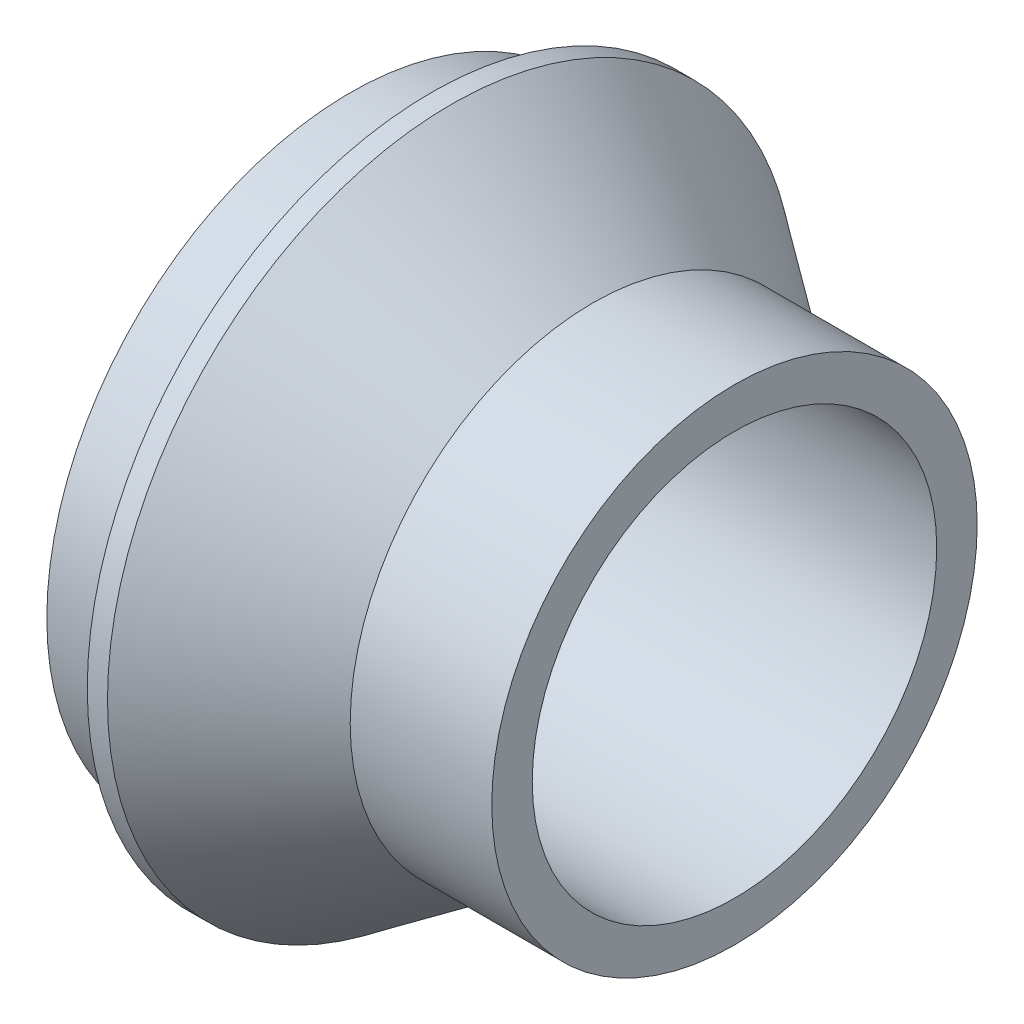
SolidWorks part; units mm, degrees
ref_plane "Płaszczyzna przednia" through (0, 0, 0) normal (0, 0, 1) x (1, 0, 0)
ref_plane "Płaszczyzna górna" through (0, 0, 0) normal (0, 1, 0) x (1, 0, 0)
ref_plane "Płaszczyzna prawa" through (0, 0, 0) normal (1, 0, 0) x (0, 0, -1)
sketch "Szkic1" plane through (0, 0, 0) normal (0, 0, 1) x (1, 0, 0)
  line L0 (0, 0) -> (42.2065, 0) construction
  line L1 (0, 15) -> (4, 15)
  line L2 (0, 13) -> (4, 13)
  line L3 (4, 13) -> (4, 10)
  line L4 (4, 10) -> (19, 10)
  line L5 (19, 10) -> (19, 12)
  line L7 (5, 17) -> (0, 17)
  line L8 (0, 17) -> (0, 13)
  line L9 (4, 15) -> (4, 17)
  line L10 (19, 12) -> (12, 12)
  line L11 (12, 12) -> (5, 17)
  dimension "D1" = 20
  dimension "D2" = 2
  dimension "D3" = 15
  dimension "D4" = 4
  dimension "D5" = 26
  dimension "D6" = 4
  dimension "D7" = 5
  dimension "D8" = 30
  dimension "D9" = 4
  dimension "D10" = 7
revolve "Obrót1" add sketch "Szkic1" angle 360 about L0
